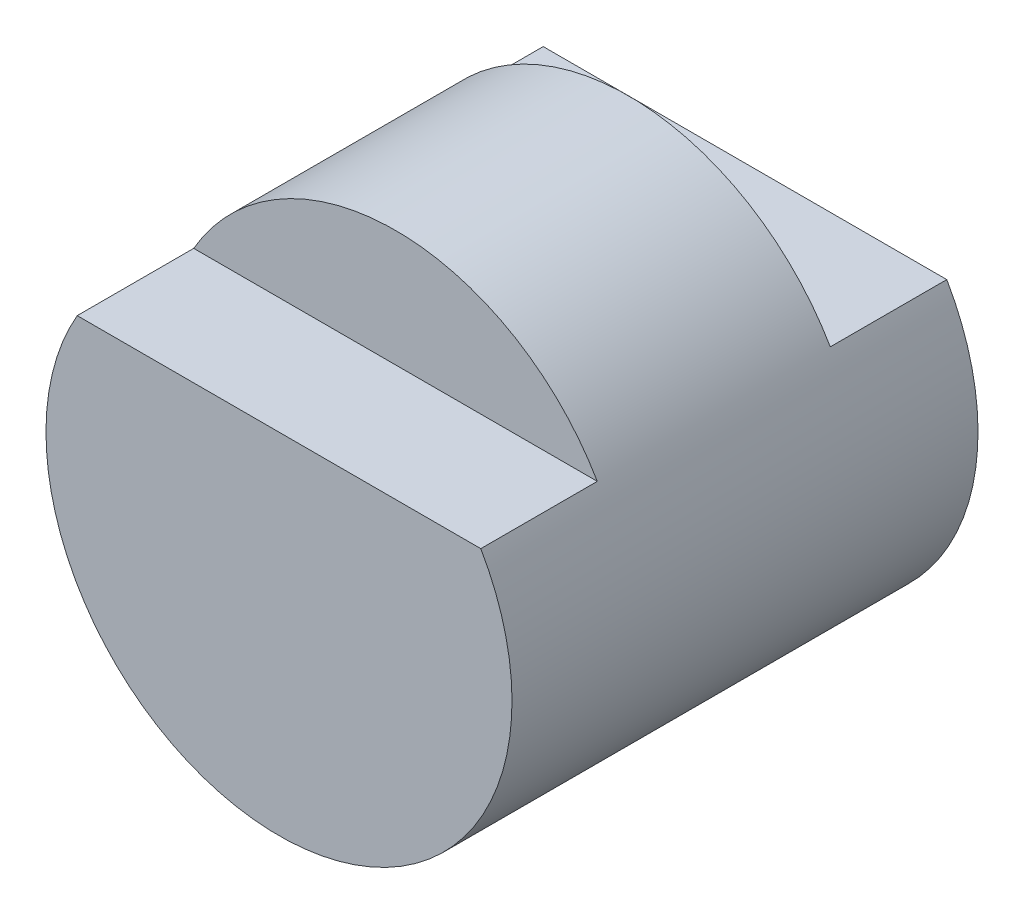
SolidWorks part; units mm, degrees
ref_plane "Front" through (0, 0, 0) normal (0, 0, 1) x (1, 0, 0)
ref_plane "Top" through (0, 0, 0) normal (0, 1, 0) x (1, 0, 0)
ref_plane "Right" through (0, 0, 0) normal (1, 0, 0) x (0, 0, -1)
sketch "Sketch1" plane through (0, 0, 0) normal (0, 0, 1) x (1, 0, 0)
  circle A0 centre (0, 0) radius 2
  dimension "D1" = 4
extrude "Boss-Extrude1" add sketch "Sketch1" along normal blind 4
sketch "Sketch2" plane through (0, 0, 4) normal (0, 0, 1) x (1, 0, 0)
  line L0 (-1.7321, 1) -> (1.7321, 1)
  circle A0 centre (0, 0) radius 2 construction
  arc A1 (-1.7321, 1) -> (1.7321, 1) centre (0, 0) cw
  dimension "D1" = 1
extrude "Cut-Extrude1" cut sketch "Sketch2" against normal blind 1
sketch "Sketch3" plane through (0, 0, 0) normal (0, 0, -1) x (-1, 0, 0)
  line L0 (1.7321, 1) -> (-1.7321, 1)
  arc A0 (1.7321, 1) -> (-1.7321, 1) centre (0, 0) ccw
extrude "Cut-Extrude2" cut sketch "Sketch3" against normal blind 1
